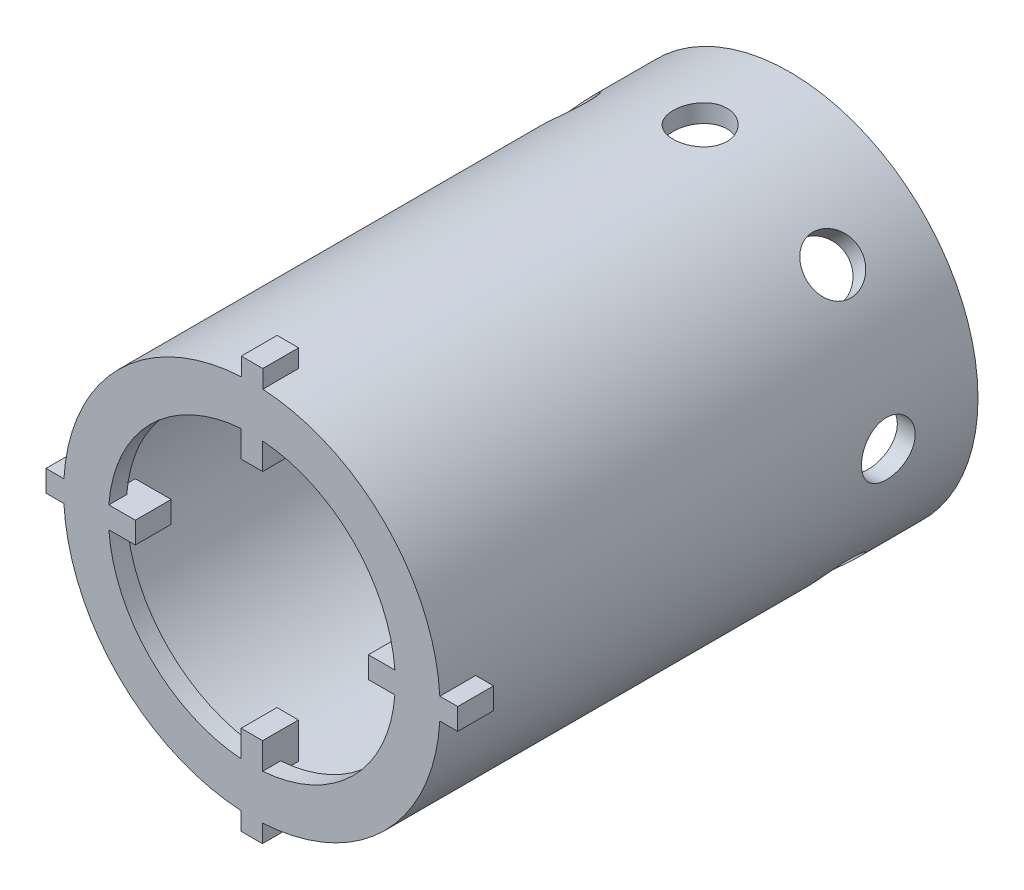
SolidWorks part; units mm, degrees
ref_plane "正面" through (0, 0, 0) normal (0, 0, 1) x (1, 0, 0)
ref_plane "平面" through (0, 0, 0) normal (0, 1, 0) x (1, 0, 0)
ref_plane "右側面" through (0, 0, 0) normal (1, 0, 0) x (0, 0, -1)
sketch "ｽｹｯﾁ1" plane through (0, 0, 0) normal (0, 0, 1) x (1, 0, 0)
  circle A0 centre (0, 0) radius 10.5
  circle A1 centre (0, 0) radius 9.5
  dimension "D1" = 21
  dimension "D2" = 19
extrude "ﾎﾞｽ - 押し出し1" add sketch "ｽｹｯﾁ1" along normal blind 30 from offset 10
sketch "ｽｹｯﾁ2" plane through (0, 0, 0) normal (0, 0, 1) x (1, 0, 0)
  circle A0 centre (0, 0) radius 10.5
  dimension "D1" = 21
extrude "ﾎﾞｽ - 押し出し2" [suppressed] add sketch "ｽｹｯﾁ2" along normal blind 1
sketch "ｽｹｯﾁ3" plane through (0, 0, 0) normal (0, 0, 1) x (1, 0, 0)
  circle A0 centre (4.4131, 3.5977) radius 0.493
extrude "ｶｯﾄ - 押し出し1" [suppressed] cut sketch "ｽｹｯﾁ3" along normal blind 1
sketch "ｽｹｯﾁ4" plane through (0, 0, 0) normal (0, 0, 1) x (1, 0, 0)
  circle A0 centre (0, 0) radius 7.5
  dimension "D1" = 15
sketch "ｽｹｯﾁ5" plane through (0, 0, 40) normal (0, 0, 1) x (1, 0, 0)
  line L1 (8.5, -0.6) -> (6.5, -0.6)
  line L2 (8.5, -0.6) -> (8.5, 0.6)
  line L3 (8.5, 0.6) -> (6.5, 0.6)
  line L4 (6.5, -0.6) -> (6.5, 0.6)
  line L5 (8.5, -0.6) -> (6.5, 0.6) construction
  line L6 (8.5, 0.6) -> (6.5, -0.6) construction
  line L7 (11.4817, -0.611) -> (9.4817, -0.611)
  line L8 (11.4817, -0.611) -> (11.4817, 0.589)
  line L9 (11.4817, 0.589) -> (9.4817, 0.589)
  line L10 (9.4817, -0.611) -> (9.4817, 0.589)
  line L11 (11.4817, -0.611) -> (9.4817, 0.589) construction
  line L12 (11.4817, 0.589) -> (9.4817, -0.611) construction
  circle A0 centre (0, 0) radius 7.5 construction
  circle A2 centre (0, 0) radius 9.5 construction
  point P0 (7.5, 0)
  point P8 (10.5, 0)
  dimension "D1" = 1.2
  dimension "D2" = 2
  dimension "D3" = 2
  dimension "D4" = 1.2
sketch "ｽｹｯﾁ6" plane through (0, 0, 0) normal (0, 0, 1) x (1, 0, 0)
  circle A0 centre (0, 0) radius 10
  circle A1 centre (0, 0) radius 8
  dimension "D1" = 20
  dimension "D2" = 16
extrude "ﾎﾞｽ - 押し出し3" add sketch "ｽｹｯﾁ6" against normal blind 1 from offset 40
extrude "ﾎﾞｽ - 押し出し4" add sketch "ｽｹｯﾁ5" against normal blind 2
pattern_circular "円形ﾊﾟﾀｰﾝ1" count 4 over 360 about axis through (0, 0, 0) along (0, 0, 1) of "ﾎﾞｽ - 押し出し4"
sketch "ｽｹｯﾁ7" plane through (0, 0, 0) normal (1, 0, 0) x (0, 0, -1)
  line L0 (-10, -10.5) -> (-10, 10.5) construction
  circle A0 centre (-15, 0) radius 1.5
  dimension "D1" = 3
  dimension "D2" = 5
extrude "ｶｯﾄ - 押し出し2" cut sketch "ｽｹｯﾁ7" against normal blind 20 and the other way blind 20
pattern_circular "円形ﾊﾟﾀｰﾝ2" count 8 over 360 about axis through (0, 0, 39) along (0, 0, 1) of "ｶｯﾄ - 押し出し2"
